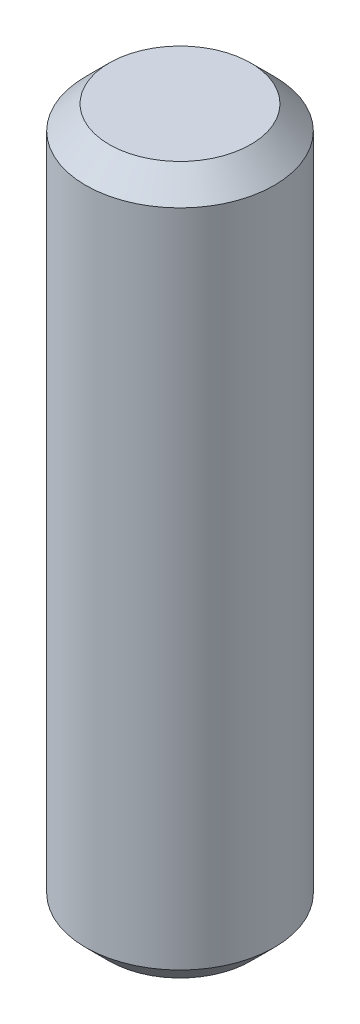
SolidWorks part; units mm, degrees
ref_plane "前基準面" through (0, 0, 0) normal (0, 0, 1) x (1, 0, 0)
ref_plane "上基準面" through (0, 0, 0) normal (0, 1, 0) x (1, 0, 0)
ref_plane "右基準面" through (0, 0, 0) normal (1, 0, 0) x (0, 0, -1)
sketch "草圖1" plane through (0, 0, 0) normal (0, 1, 0) x (1, 0, 0)
  circle A0 centre (0, 0) radius 2
  dimension "D1" = 4
extrude "填料-伸長1" add sketch "草圖1" along normal blind 15
chamfer "導角1" distance 0.5 angle 45 1 edges at (0, 15, 2)
chamfer "導角2" distance 0.5 angle 45 1 edges at (0, 0, 2)
